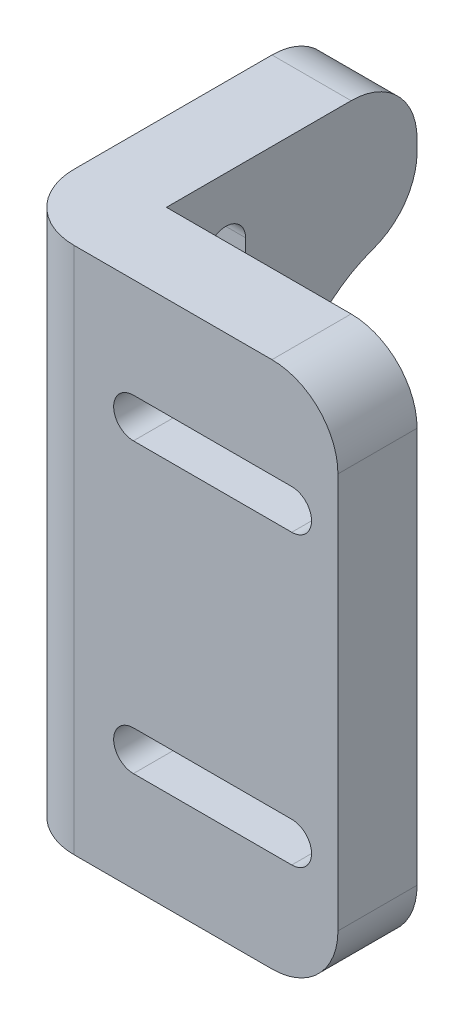
SolidWorks part; units mm, degrees
ref_plane "Front Plane" through (0, 0, 0) normal (0, 0, 1) x (1, 0, 0)
ref_plane "Top Plane" through (0, 0, 0) normal (0, 1, 0) x (1, 0, 0)
ref_plane "Right Plane" through (0, 0, 0) normal (1, 0, 0) x (0, 0, -1)
sketch "Sketch1" plane through (0, 0, 0) normal (0, 1, 0) x (1, 0, 0)
  line L1 (-12.5, 3) -> (12.5, 3)
  line L2 (-12.5, 3) -> (-12.5, -3)
  line L3 (-12.5, -3) -> (12.5, -3)
  line L4 (12.5, 3) -> (12.5, -3)
  line L5 (-12.5, 3) -> (12.5, -3) construction
  line L6 (-12.5, -3) -> (12.5, 3) construction
  line L7 (-12.5, -3) -> (-6.5, -3)
  line L8 (-12.5, -3) -> (-12.5, 22)
  line L9 (-12.5, 22) -> (-6.5, 22)
  line L10 (-6.5, -3) -> (-6.5, 22)
  point P0 (0, 0)
  dimension "D1" = 25
  dimension "D2" = 6
  dimension "D3" = 25
extrude "Boss-Extrude1" add sketch "Sketch1" along normal blind 40 contours L1 L10 L9 L8 | L3 L10 L1 L2 | L10 L3 L4 L1
sketch "Sketch2" plane through (-6.5, 0, 0) normal (1, 0, 0) x (0, 0, -1)
  line L0 (3, 20) -> (12, 20) construction
  line L1 (7.5, 20) -> (7.5, 40) construction
  line L4 (22, 40) -> (22, 0) construction
  line L6 (3, 40) -> (22, 40) construction
  line L7 (7.5, 35) -> (7.5, 25) construction
  line L8 (9, 35) -> (9, 25)
  line L9 (6, 35) -> (6, 25)
  line L10 (7.5, 5) -> (7.5, 15) construction
  line L13 (3, 40) -> (3, 0) construction
  line L14 (9, 5) -> (9, 15)
  line L15 (6, 5) -> (6, 15)
  circle A3 centre (22, 20) radius 10
  arc A5 (9, 35) -> (6, 35) centre (7.5, 35) ccw
  arc A6 (6, 25) -> (9, 25) centre (7.5, 25) ccw
  arc A9 (9, 5) -> (6, 5) centre (7.5, 5) cw
  arc A10 (6, 15) -> (9, 15) centre (7.5, 15) cw
  point P12 (7.5, 30)
  point P18 (0, 0)
  point P19 (0, 0)
  point P21 (7.5, 30)
  point P24 (7.5, 10)
  dimension "D1" = 1.5
  dimension "D2" = 10
extrude "Cut-Extrude1" cut sketch "Sketch2" against normal up to next
sketch "Sketch3" plane through (0, 0, 3) normal (0, 0, -1) x (-1, 0, 0)
  line L0 (-3, 40) -> (-3, 0) construction
  line L1 (-12.5, 40) -> (-12.5, 0) construction
  line L3 (-3, 30.92) -> (-3, 9.08) construction
  line L4 (6.5, 40) -> (-12.5, 40) construction
  line L5 (-9, 30.92) -> (3, 30.92) construction
  line L8 (-9, 32.42) -> (3, 32.42)
  line L9 (-9, 29.42) -> (3, 29.42)
  line L10 (-9, 9.08) -> (3, 9.08) construction
  line L11 (-9, 10.58) -> (3, 10.58)
  line L12 (-9, 7.58) -> (3, 7.58)
  line L13 (6.5, 0) -> (-12.5, 0) construction
  line L14 (-3, 20) -> (6.5, 20) construction
  line L15 (6.5, 30) -> (6.5, 10) construction
  arc A2 (-9, 32.42) -> (-9, 29.42) centre (-9, 30.92) ccw
  arc A3 (3, 29.42) -> (3, 32.42) centre (3, 30.92) ccw
  arc A4 (-9, 10.58) -> (-9, 7.58) centre (-9, 9.08) ccw
  arc A5 (3, 7.58) -> (3, 10.58) centre (3, 9.08) ccw
  point P12 (-3, 30.92)
  point P20 (-3, 9.08)
  point P29 (-3, 20)
  dimension "D2" = 3
  dimension "D1" = 3.5
  dimension "D3" = 21.84
  dimension "D4" = 2
extrude "Cut-Extrude2" cut sketch "Sketch3" along normal up to next contours L9 A2 L8 A3 | L11 A5 L12 A4
sketch "Sketch4" plane through (0, 0, -3) normal (0, 0, -1) x (-1, 0, 0)
  line L0 (-3, 32.42) -> (-3, 29.42) construction
  line L1 (-9, 32.42) -> (3, 32.42) construction
  line L2 (-9, 29.42) -> (3, 29.42) construction
  line L3 (-12.5, 20) -> (6.5, 20) construction
  line L4 (-9, 9.08) -> (3, 9.08) construction
  line L5 (-9, 6.33) -> (3, 6.33)
  line L6 (-12.5, 40) -> (-12.5, 0) construction
  line L7 (6.5, 40) -> (6.5, 0) construction
  line L8 (-9, 30.92) -> (3, 30.92) construction
  line L9 (-9, 33.67) -> (3, 33.67)
  line L10 (-9, 28.17) -> (3, 28.17)
  line L11 (-9, 11.83) -> (3, 11.83)
  arc A0 (-9, 33.67) -> (-9, 28.17) centre (-9, 30.92) ccw
  arc A1 (3, 28.17) -> (3, 33.67) centre (3, 30.92) ccw
  arc A4 (-9, 6.33) -> (-9, 11.83) centre (-9, 9.08) cw
  arc A5 (3, 11.83) -> (3, 6.33) centre (3, 9.08) cw
  point P14 (-3, 30.92)
  point P19 (0, 0)
  point P20 (-3, 30.92)
  point P23 (-3, 9.08)
  dimension "D1" = 2.75
extrude "Cut-Extrude3" cut sketch "Sketch4" against normal blind 3
fillet "Fillet1" radius 5 7 edges at (-12.5, 20, 3) (-9.5, 0, -22) (-9.5, 40, -22) (-9.5, 10, -22) (-9.5, 30, -22) (12.5, 0, 0) (12.5, 40, 0)
